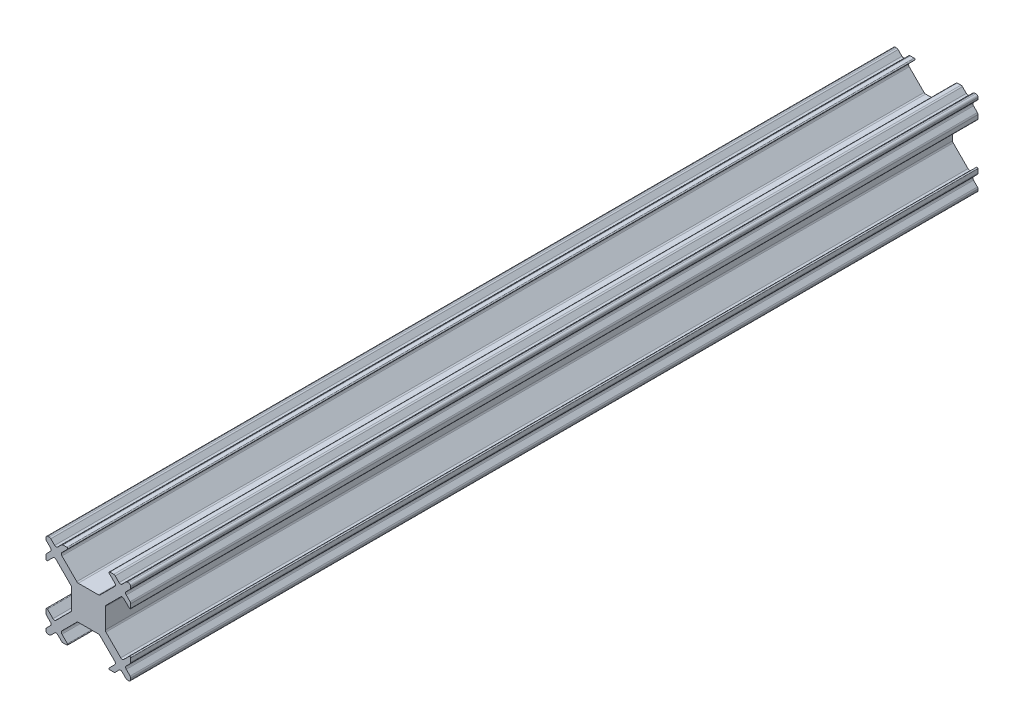
SolidWorks part; units mm, degrees
ref_plane "Front Plane" through (0, 0, 0) normal (0, 0, 1) x (1, 0, 0)
ref_plane "Top Plane" through (0, 0, 0) normal (0, 1, 0) x (1, 0, 0)
ref_plane "Right Plane" through (0, 0, 0) normal (1, 0, 0) x (0, 0, -1)
sketch "Sketch1" plane through (0, 0, 0) normal (0, 0, 1) x (1, 0, 0)
  line L0 (-26.4346, 28.4965) -> (-25.9796, 28.9515)
  line L1 (-25.1311, 29.8) -> (-24.676, 30.2551)
  line L2 (-24.676, 20.4015) -> (-25.1311, 20.8565)
  line L3 (-25.9796, 21.7051) -> (-26.4346, 22.1601)
  line L4 (-26.5078, 30.0783) -> (-26.5078, 29.9369)
  line L5 (-26.5078, 28.3197) -> (-26.5078, 27.8626)
  line L6 (-26.5078, 22.794) -> (-26.5078, 22.3369)
  line L7 (-26.5078, 20.7197) -> (-26.5078, 20.5783)
  line L8 (-23.9714, 30.1576) -> (-24.624, 29.5051)
  line L9 (-25.6846, 28.4444) -> (-26.3371, 27.7919)
  line L10 (-26.2578, 20.3283) -> (-26.1164, 20.3283)
  line L11 (-24.4993, 20.3283) -> (-24.0422, 20.3283)
  line L12 (-18.9735, 20.3283) -> (-18.5164, 20.3283)
  line L13 (-16.8993, 20.3283) -> (-16.7578, 20.3283)
  line L14 (-26.3371, 22.8647) -> (-25.6846, 22.2122)
  line L15 (-24.624, 21.1515) -> (-23.9714, 20.499)
  line L16 (-23.5078, 26.5176) -> (-23.5078, 24.139)
  line L17 (-22.6972, 23.3283) -> (-20.3185, 23.3283)
  line L18 (-25.3311, 22.2122) -> (-23.5811, 23.9622)
  line L19 (-20.1417, 27.4015) -> (-18.3917, 29.1515)
  line L20 (-18.3917, 21.5051) -> (-20.1417, 23.2551)
  line L21 (-23.5811, 26.6944) -> (-25.3311, 28.4444)
  line L22 (-26.4346, 20.8965) -> (-25.9796, 21.3515)
  line L23 (-17.5311, 29.8) -> (-17.076, 30.2551)
  line L24 (-17.076, 20.4015) -> (-17.5311, 20.8565)
  line L25 (-25.9796, 29.3051) -> (-26.4346, 29.7601)
  line L26 (-16.5811, 29.7601) -> (-17.0361, 29.3051)
  line L27 (-25.4846, 20.8565) -> (-25.9396, 20.4015)
  line L28 (-17.6846, 28.4444) -> (-19.4346, 26.6944)
  line L29 (-22.874, 23.2551) -> (-24.624, 21.5051)
  line L30 (-25.9396, 30.2551) -> (-25.4846, 29.8)
  line L31 (-17.0361, 21.3515) -> (-16.5811, 20.8965)
  line L32 (-24.624, 29.1515) -> (-22.874, 27.4015)
  line L33 (-19.4346, 23.9622) -> (-17.6846, 22.2122)
  line L34 (-19.5078, 24.139) -> (-19.5078, 26.5176)
  line L35 (-20.3185, 27.3283) -> (-22.6972, 27.3283)
  line L36 (-16.5078, 20.5783) -> (-16.5078, 20.7197)
  line L37 (-16.5078, 22.3369) -> (-16.5078, 22.794)
  line L38 (-16.5078, 27.8626) -> (-16.5078, 28.3197)
  line L39 (-16.5078, 29.9369) -> (-16.5078, 30.0783)
  line L40 (-16.7578, 30.3283) -> (-16.8993, 30.3283)
  line L41 (-18.5164, 30.3283) -> (-18.9735, 30.3283)
  line L42 (-24.0422, 30.3283) -> (-24.4993, 30.3283)
  line L43 (-26.1164, 30.3283) -> (-26.2578, 30.3283)
  line L44 (-19.0442, 20.499) -> (-18.3917, 21.1515)
  line L45 (-17.3311, 22.2122) -> (-16.6786, 22.8647)
  line L46 (-16.6786, 27.7919) -> (-17.3311, 28.4444)
  line L47 (-18.3917, 29.5051) -> (-19.0442, 30.1576)
  line L48 (-16.5811, 22.1601) -> (-17.0361, 21.7051)
  line L49 (-17.8846, 20.8565) -> (-18.3396, 20.4015)
  line L50 (-18.3396, 30.2551) -> (-17.8846, 29.8)
  line L51 (-17.0361, 28.9515) -> (-16.5811, 28.4965)
  arc A0 (-16.5078, 30.0783) -> (-16.7578, 30.3283) centre (-16.7578, 30.0783) ccw
  arc A1 (-26.2578, 30.3283) -> (-26.5078, 30.0783) centre (-26.2578, 30.0783) ccw
  arc A2 (-16.7578, 20.3283) -> (-16.5078, 20.5783) centre (-16.7578, 20.5783) ccw
  arc A3 (-26.5078, 20.5783) -> (-26.2578, 20.3283) centre (-26.2578, 20.5783) ccw
  arc A4 (-18.9735, 30.3283) -> (-19.0442, 30.1576) centre (-18.9735, 30.2283) ccw
  arc A5 (-16.6786, 27.7919) -> (-16.5078, 27.8626) centre (-16.6078, 27.8626) ccw
  arc A6 (-16.5078, 22.794) -> (-16.6786, 22.8647) centre (-16.6078, 22.794) ccw
  arc A7 (-19.0442, 20.499) -> (-18.9735, 20.3283) centre (-18.9735, 20.4283) ccw
  arc A8 (-26.3371, 22.8647) -> (-26.5078, 22.794) centre (-26.4078, 22.794) ccw
  arc A9 (-26.5078, 27.8626) -> (-26.3371, 27.7919) centre (-26.4078, 27.8626) ccw
  arc A10 (-23.9714, 30.1576) -> (-24.0422, 30.3283) centre (-24.0422, 30.2283) ccw
  arc A11 (-24.0422, 20.3283) -> (-23.9714, 20.499) centre (-24.0422, 20.4283) ccw
  arc A12 (-22.874, 27.4015) -> (-22.6972, 27.3283) centre (-22.6972, 27.5783) ccw
  arc A13 (-20.3185, 27.3283) -> (-20.1417, 27.4015) centre (-20.3185, 27.5783) ccw
  arc A14 (-19.5078, 24.139) -> (-19.4346, 23.9622) centre (-19.2578, 24.139) ccw
  arc A15 (-17.6846, 22.2122) -> (-17.3311, 22.2122) centre (-17.5078, 22.389) ccw
  arc A16 (-22.6972, 23.3283) -> (-22.874, 23.2551) centre (-22.6972, 23.0783) ccw
  arc A17 (-20.1417, 23.2551) -> (-20.3185, 23.3283) centre (-20.3185, 23.0783) ccw
  arc A18 (-25.3311, 28.4444) -> (-25.6846, 28.4444) centre (-25.5078, 28.2676) ccw
  arc A19 (-23.5811, 23.9622) -> (-23.5078, 24.139) centre (-23.7578, 24.139) ccw
  arc A20 (-23.5078, 26.5176) -> (-23.5811, 26.6944) centre (-23.7578, 26.5176) ccw
  arc A21 (-25.6846, 22.2122) -> (-25.3311, 22.2122) centre (-25.5078, 22.389) ccw
  arc A22 (-24.624, 21.5051) -> (-24.624, 21.1515) centre (-24.4472, 21.3283) ccw
  arc A23 (-18.3917, 21.1515) -> (-18.3917, 21.5051) centre (-18.5685, 21.3283) ccw
  arc A24 (-18.3917, 29.1515) -> (-18.3917, 29.5051) centre (-18.5685, 29.3283) ccw
  arc A25 (-17.3311, 28.4444) -> (-17.6846, 28.4444) centre (-17.5078, 28.2676) ccw
  arc A26 (-19.4346, 26.6944) -> (-19.5078, 26.5176) centre (-19.2578, 26.5176) ccw
  arc A27 (-24.624, 29.5051) -> (-24.624, 29.1515) centre (-24.4472, 29.3283) ccw
  arc A28 (-17.0361, 29.3051) -> (-17.0361, 28.9515) centre (-16.8593, 29.1283) ccw
  arc A29 (-17.0361, 21.7051) -> (-17.0361, 21.3515) centre (-16.8593, 21.5283) ccw
  arc A30 (-25.4846, 29.8) -> (-25.1311, 29.8) centre (-25.3078, 29.9768) ccw
  arc A31 (-17.8846, 29.8) -> (-17.5311, 29.8) centre (-17.7078, 29.9768) ccw
  arc A32 (-25.9796, 28.9515) -> (-25.9796, 29.3051) centre (-26.1564, 29.1283) ccw
  arc A33 (-25.9796, 21.3515) -> (-25.9796, 21.7051) centre (-26.1564, 21.5283) ccw
  arc A34 (-17.5311, 20.8565) -> (-17.8846, 20.8565) centre (-17.7078, 20.6798) ccw
  arc A35 (-25.1311, 20.8565) -> (-25.4846, 20.8565) centre (-25.3078, 20.6798) ccw
  arc A36 (-18.3396, 30.2551) -> (-18.5164, 30.3283) centre (-18.5164, 30.0783) ccw
  arc A37 (-16.8993, 30.3283) -> (-17.076, 30.2551) centre (-16.8993, 30.0783) ccw
  arc A38 (-24.4993, 30.3283) -> (-24.676, 30.2551) centre (-24.4993, 30.0783) ccw
  arc A39 (-25.9396, 30.2551) -> (-26.1164, 30.3283) centre (-26.1164, 30.0783) ccw
  arc A40 (-26.5078, 29.9369) -> (-26.4346, 29.7601) centre (-26.2578, 29.9369) ccw
  arc A41 (-26.4346, 28.4965) -> (-26.5078, 28.3197) centre (-26.2578, 28.3197) ccw
  arc A42 (-26.4346, 20.8965) -> (-26.5078, 20.7197) centre (-26.2578, 20.7197) ccw
  arc A43 (-26.5078, 22.3369) -> (-26.4346, 22.1601) centre (-26.2578, 22.3369) ccw
  arc A44 (-24.676, 20.4015) -> (-24.4993, 20.3283) centre (-24.4993, 20.5783) ccw
  arc A45 (-18.5164, 20.3283) -> (-18.3396, 20.4015) centre (-18.5164, 20.5783) ccw
  arc A46 (-17.076, 20.4015) -> (-16.8993, 20.3283) centre (-16.8993, 20.5783) ccw
  arc A47 (-16.5078, 28.3197) -> (-16.5811, 28.4965) centre (-16.7578, 28.3197) ccw
  arc A48 (-16.5078, 20.7197) -> (-16.5811, 20.8965) centre (-16.7578, 20.7197) ccw
  arc A49 (-16.5811, 22.1601) -> (-16.5078, 22.3369) centre (-16.7578, 22.3369) ccw
  arc A50 (-16.5811, 29.7601) -> (-16.5078, 29.9369) centre (-16.7578, 29.9369) ccw
  arc A51 (-26.1164, 20.3283) -> (-25.9396, 20.4015) centre (-26.1164, 20.5783) ccw
  dimension "D1" = 4
  dimension "D2" = 10
extrude "Boss-Extrude1" add sketch "Sketch1" along normal blind 100
